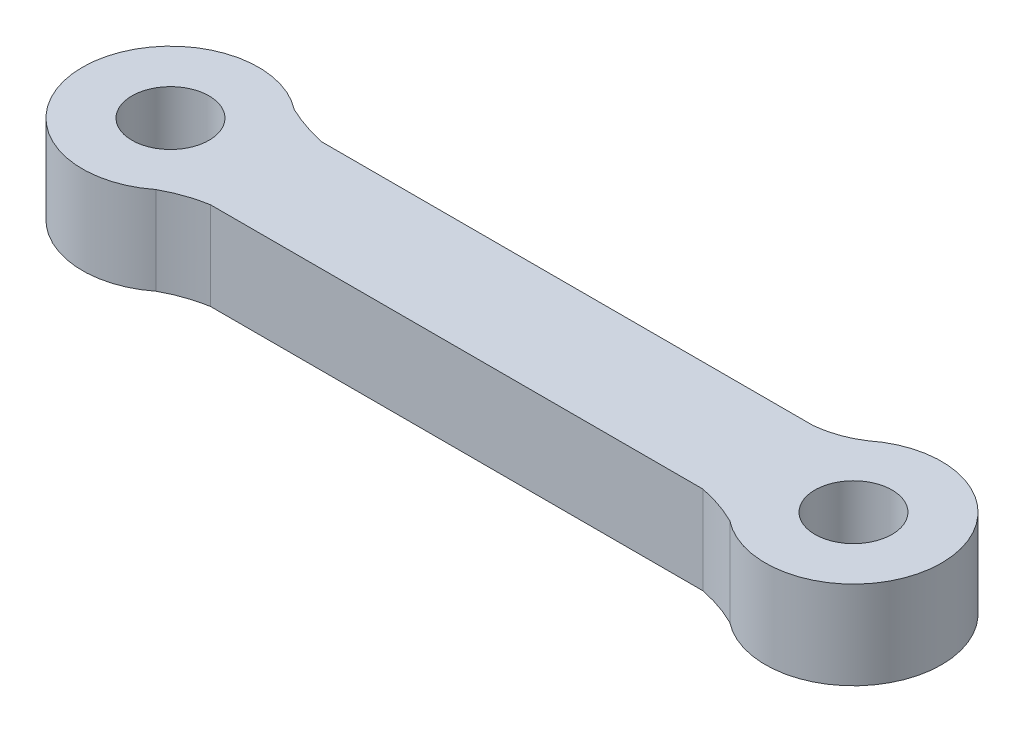
SolidWorks part; units mm, degrees
ref_plane "Alzado" through (0, 0, 0) normal (0, 0, 1) x (1, 0, 0)
ref_plane "Planta" through (0, 0, 0) normal (0, 1, 0) x (1, 0, 0)
ref_plane "Vista lateral" through (0, 0, 0) normal (1, 0, 0) x (0, 0, -1)
sketch "Croquis1" plane through (0, 0, 0) normal (0, 1, 0) x (1, 0, 0)
  line L1 (-11.1671, 2.4995) -> (11.1719, 2.4995)
  line L3 (-11.1767, -2.5005) -> (11.1719, -2.5005)
  line L5 (-11.1671, 2.4995) -> (11.1719, -2.5005) construction
  line L6 (-11.1767, -2.5005) -> (11.1719, 2.4995) construction
  arc A0 (-13.0255, 3.1431) -> (-13.0255, -3.1431) centre (-15.4995, 0) ccw
  arc A1 (13.0279, -3.1355) -> (13.0146, 3.1403) centre (15.5019, 0.0076) ccw
  circle A2 centre (-15.4995, 0) radius 1.75
  circle A3 centre (15.5019, 0.0076) radius 1.75
  spline S0 degree 2 poles (-11.1671, 2.4995) (-12.1502, 2.7277) (-13.0255, 3.1431) knots 0 0 0 0.309193 0.309193 0.309193
  spline S1 degree 2 poles (-11.1767, -2.5005) (-12.1815, -2.6733) (-13.0255, -3.1431) knots 0 0 0 0.480047 0.480047 0.480047
  spline S2 degree 2 poles (11.1719, -2.5005) (12.1634, -2.7001) (13.0279, -3.1355) knots 0 0 0 0.381033 0.381033 0.381033
  spline S3 degree 2 poles (11.1719, 2.4995) (12.2078, 2.6089) (13.0146, 3.1403) knots 0 0 0 0.652329 0.652329 0.652329
  point P0 (0, 0)
  point P13 (13.0146, 3.1403)
  point P14 (13.0279, -3.1355)
  point P17 (-13.0255, 3.1431)
  point P18 (-13.0255, -3.1431)
  dimension "D3" = 3.5
  dimension "D4" = 8
  dimension "D5" = 8
  dimension "D6" = 3.5
  dimension "D7" = 1.97
  dimension "D1" = 5
  dimension "D2" = 22.339
extrude "Saliente-Extruir1" add sketch "Croquis1" along normal blind 4
